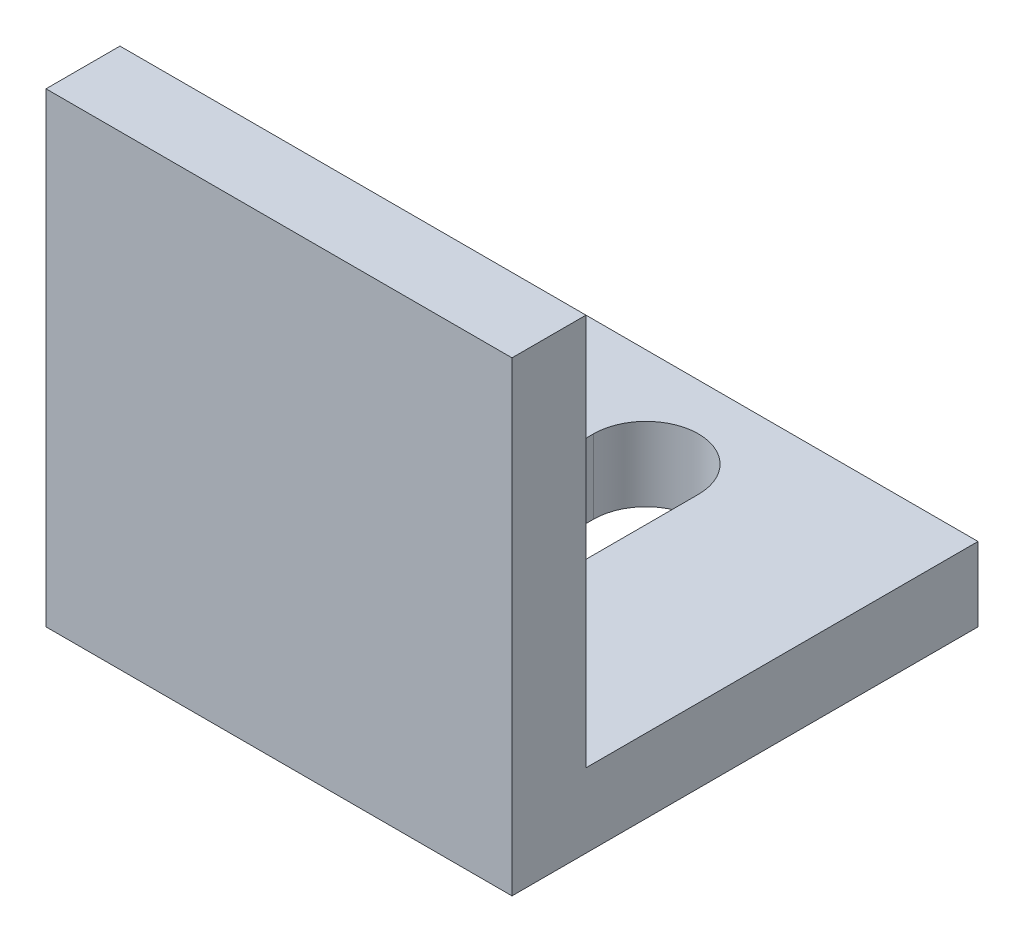
SolidWorks part; units mm, degrees
ref_plane "Front Plane" through (0, 0, 0) normal (0, 0, 1) x (1, 0, 0)
ref_plane "Top Plane" through (0, 0, 0) normal (0, 1, 0) x (1, 0, 0)
ref_plane "Right Plane" through (0, 0, 0) normal (1, 0, 0) x (0, 0, -1)
sketch "Sketch1" plane through (0, 0, 0) normal (1, 0, 0) x (0, 0, -1)
  line L0 (0, 0) -> (0, 20)
  line L1 (0, 55) -> (0, -55) construction
  line L2 (0, 20) -> (3.175, 20)
  line L3 (3.175, 20) -> (3.175, 3.175)
  line L4 (3.175, 3.175) -> (20, 3.175)
  line L5 (20, 3.175) -> (20, 0)
  line L6 (55, 0) -> (-55, 0) construction
  line L7 (0, 0) -> (20, 0)
  dimension "D1" = 20
  dimension "D2" = 20
  dimension "D3" = 3.175
  dimension "D4" = 3.175
extrude "Boss-Extrude1" add sketch "Sketch1" along normal blind 20
sketch "Sketch2" plane through (0, 0, 0) normal (0, -1, 0) x (-1, 0, 0)
  line L4 (-7.75, 15.75) -> (-7.75, 5.75)
  line L6 (-12.25, 15.75) -> (-12.25, 5.75)
  line L7 (-20, 0) -> (-20, 20) construction
  line L8 (-10, 0) -> (-10, 23.8536) construction
  line L9 (-20, 0) -> (0, 0) construction
  line L10 (-20, 10) -> (6.7384, 10) construction
  line L11 (-20, 20) -> (0, 20) construction
  arc A1 (-12.25, 15.75) -> (-7.75, 15.75) centre (-10, 15.75) cw
  arc A2 (-12.25, 5.75) -> (-7.75, 5.75) centre (-10, 5.75) ccw
  point P13 (-10, 18)
  point P14 (-10, 3.5)
  dimension "D1" = 4.5
  dimension "D2" = 0
  dimension "D3" = 10
  dimension "D4" = 3.5
  dimension "D5" = 2
extrude "Cut-Extrude1" cut sketch "Sketch2" against normal through all
